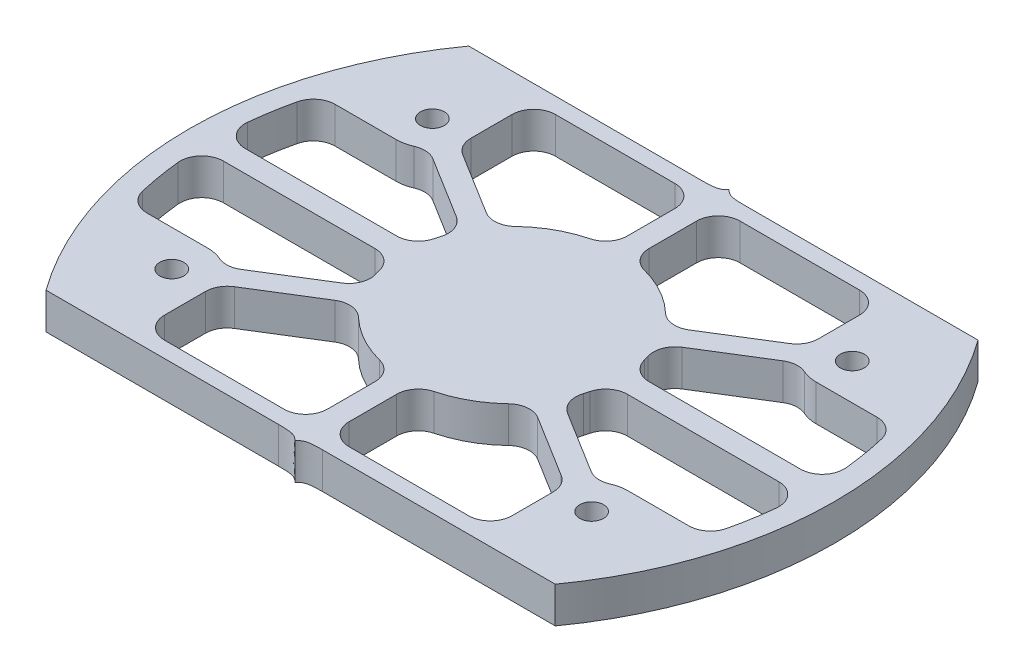
SolidWorks part; units mm, degrees
material "3.1355 (EN-AW 2024)"
ref_plane "Front" through (0, 0, 0) normal (0, 0, 1) x (1, 0, 0)
ref_plane "Top" through (0, 0, 0) normal (0, 1, 0) x (1, 0, 0)
ref_plane "Right" through (0, 0, 0) normal (1, 0, 0) x (0, 0, -1)
sketch "Эскиз1" plane through (0, 0, 0) normal (0, 1, 0) x (1, 0, 0)
  line L0 (0, 0) -> (0, 60) construction
  line L1 (0, 60) -> (10, 60) construction
  line L3 (79.1655, 0) -> (10, 0)
  line L4 (0, 30) -> (63.0426, 30) construction
  line L5 (10, 60) -> (79.1655, 60)
  line L6 (10, 0) -> (0, 0) construction
  line L7 (15.5828, 48) -> (73.5828, 48) construction
  line L8 (15.5828, 12) -> (73.5828, 12) construction
  line L9 (44.5828, 60) -> (44.5828, 0) construction
  arc A0 (10, 0) -> (10, 60) centre (50, 30) cw
  arc A1 (79.1655, 0) -> (79.1655, 60) centre (39.1655, 30) ccw
  point P5 (15.5828, 48)
  dimension "D3" = 50
  dimension "D1" = 60
  dimension "D2" = 12
  dimension "D4" = 38.84
  dimension "D5" = 58
extrude "Бобышка-Вытянуть1" add sketch "Эскиз1" along normal blind 5
sketch "Эскиз2" plane through (0, 5, 0) normal (0, 1, 0) x (1, 0, 0)
  line L4 (11.5292, 3) -> (77.6363, 3)
  line L5 (77.6363, 57) -> (11.5292, 57)
  line L6 (11.5292, 3) -> (77.6363, 3)
  line L7 (77.6363, 57) -> (11.5292, 57)
  arc A4 (11.5292, 57) -> (11.5292, 3) centre (50, 30) ccw
  arc A5 (77.6363, 3) -> (77.6363, 57) centre (39.1655, 30) ccw
  arc A6 (11.5292, 57) -> (11.5292, 3) centre (50, 30) ccw
  arc A7 (77.6363, 3) -> (77.6363, 57) centre (39.1655, 30) ccw
  dimension "D1" = 3
extrude "Вырез-Вытянуть1" cut sketch "Эскиз2" against normal through all
sketch "Эскиз3" plane through (0, 5, 0) normal (0, 1, 0) x (1, 0, 0)
  line L1 (89.1655, 30) -> (0, 30) construction
  circle A0 centre (15.5828, 48) radius 5
  circle A1 centre (73.5828, 48) radius 5
  arc A2 (79.1655, 0) -> (79.1655, 60) centre (39.1655, 30) ccw construction
  circle A3 centre (73.5828, 12) radius 5
  circle A4 centre (15.5828, 12) radius 5
  circle A5 centre (44.5828, 30) radius 15
  dimension "D1" = 10
  dimension "D2" = 10
  dimension "D3" = 30
extrude "Бобышка-Вытянуть2" add sketch "Эскиз3" against normal through all separate body
sketch "Эскиз4" plane through (0, 5, 0) normal (0, 1, 0) x (1, 0, 0)
  line L0 (77.6363, 57) -> (11.5292, 57) construction
  line L1 (11.5292, 3) -> (77.6363, 3) construction
  line L2 (77.6363, 57) -> (11.5292, 57) construction
  line L3 (11.5292, 3) -> (77.6363, 3) construction
  line L4 (44.5828, 45) -> (44.5828, 57) construction
  line L5 (31.8382, 37.9104) -> (19.831, 45.3632) construction
  line L6 (57.3274, 37.9104) -> (69.3346, 45.3632) construction
  line L7 (3, 30) -> (29.5828, 30) construction
  line L8 (86.1655, 30) -> (59.5828, 30) construction
  line L9 (57.3274, 22.0896) -> (69.3346, 14.6368) construction
  line L10 (31.8382, 22.0896) -> (19.831, 14.6368) construction
  line L11 (44.5828, 15) -> (44.5828, 3) construction
  line L12 (46.0828, 44.9248) -> (46.0828, 57)
  line L13 (32.6931, 39.1453) -> (20.4263, 46.7591)
  line L14 (58.0545, 36.5963) -> (70.3213, 44.2102)
  line L15 (56.4724, 20.8547) -> (68.7392, 13.2409)
  line L16 (43.0828, 15.0752) -> (43.0828, 3)
  line L17 (31.111, 23.4037) -> (18.8443, 15.7898)
  line L18 (43.0828, 44.9248) -> (43.0828, 57)
  line L19 (31.111, 36.5963) -> (18.8443, 44.2102)
  line L20 (56.4724, 39.1453) -> (68.7392, 46.7591)
  line L21 (58.0545, 23.4037) -> (70.3213, 15.7898)
  line L22 (46.0828, 15.0752) -> (46.0828, 3)
  line L23 (32.6931, 20.8547) -> (20.4263, 13.2409)
  line L24 (32.6292, 39.1849) -> (20.622, 46.6376) construction
  line L25 (31.0471, 36.636) -> (19.0399, 44.0887) construction
  line L26 (43.0828, 45) -> (43.0828, 57) construction
  line L27 (46.0828, 45) -> (46.0828, 57) construction
  line L28 (56.5363, 39.1849) -> (68.5435, 46.6376) construction
  line L29 (58.1184, 36.636) -> (70.1256, 44.0887) construction
  line L30 (58.1184, 23.364) -> (70.1256, 15.9113) construction
  line L31 (56.5363, 20.8151) -> (68.5435, 13.3624) construction
  line L32 (46.0828, 15) -> (46.0828, 3) construction
  line L33 (43.0828, 15) -> (43.0828, 3) construction
  line L34 (32.6292, 20.8151) -> (20.622, 13.3624) construction
  line L35 (31.0471, 23.364) -> (19.0399, 15.9113) construction
  line L36 (3.0239, 28.5) -> (29.658, 28.5)
  line L37 (86.1416, 31.5) -> (59.5076, 31.5)
  line L38 (3.0239, 31.5) -> (29.658, 31.5)
  line L39 (86.1416, 28.5) -> (59.5076, 28.5)
  line L40 (3, 31.5) -> (29.5828, 31.5) construction
  line L41 (3, 28.5) -> (29.5828, 28.5) construction
  line L42 (86.1655, 31.5) -> (59.5828, 31.5) construction
  line L43 (86.1655, 28.5) -> (59.5828, 28.5) construction
  line L44 (43.0828, 57) -> (46.0828, 57)
  line L45 (3.0239, 31.5) -> (2.4021, 31.5)
  line L46 (2.4021, 31.5) -> (2.4021, 28.5)
  line L47 (2.4021, 28.5) -> (3.0239, 28.5)
  line L48 (3.0239, 28.5) -> (2.938, 28.4918)
  line L49 (86.1416, 31.5) -> (86.6727, 31.5)
  line L50 (86.6727, 31.5) -> (86.6727, 28.5)
  line L51 (86.6727, 28.5) -> (86.1416, 28.5)
  line L52 (43.0828, 3) -> (46.0828, 3)
  arc A0 (11.5292, 57) -> (11.5292, 3) centre (50, 30) ccw construction
  circle A1 centre (44.5828, 30) radius 15
  arc A2 (43.0828, 15.0752) -> (46.0828, 15.0752) centre (44.5828, 30) ccw
  arc A3 (77.6363, 3) -> (77.6363, 57) centre (39.1655, 30) ccw construction
  arc A4 (11.5292, 57) -> (11.5292, 3) centre (50, 30) ccw construction
  arc A5 (77.6363, 3) -> (77.6363, 57) centre (39.1655, 30) ccw construction
  circle A6 centre (73.5828, 48) radius 5 construction
  circle A7 centre (73.5828, 12) radius 5 construction
  circle A8 centre (15.5828, 12) radius 5 construction
  circle A9 centre (15.5828, 48) radius 5 construction
  arc A10 (68.7392, 46.7591) -> (70.3213, 44.2102) centre (73.5828, 48) ccw
  arc A11 (70.3213, 15.7898) -> (68.7392, 13.2409) centre (73.5828, 12) ccw
  arc A12 (20.4263, 13.2409) -> (18.8443, 15.7898) centre (15.5828, 12) ccw
  arc A13 (18.8443, 44.2102) -> (20.4263, 46.7591) centre (15.5828, 48) ccw
  arc A14 (56.4724, 20.8547) -> (58.0545, 23.4037) centre (44.5828, 30) ccw
  arc A15 (31.111, 23.4037) -> (32.6931, 20.8547) centre (44.5828, 30) ccw
  arc A16 (59.5076, 28.5) -> (59.5076, 31.5) centre (44.5828, 30) ccw
  arc A17 (58.0545, 36.5963) -> (56.4724, 39.1453) centre (44.5828, 30) ccw
  arc A18 (29.658, 31.5) -> (29.658, 28.5) centre (44.5828, 30) ccw
  arc A19 (32.6931, 39.1453) -> (31.111, 36.5963) centre (44.5828, 30) ccw
  arc A20 (46.0828, 44.9248) -> (43.0828, 44.9248) centre (44.5828, 30) ccw
  circle M2 centre (44.5828, 30) radius 15
  dimension "D1" = 0
  dimension "D2" = 1.5
  dimension "D3" = 1.5
  dimension "D4" = 1.5
  dimension "D5" = 1.5
extrude "Бобышка-Вытянуть3" add sketch "Эскиз4" against normal through all contours A13 L19 L13 M2 | L44 L18 L12 M2 | A10 L20 L14 M2 | L51 L50 L49 L37 L39 M2 | A11 L21 L15 M2 | L16 L52 L22 M2 | A12 L23 L17 M2 | L46 L47 L36 L38 L45 M2
sketch "Эскиз5" plane through (0, 0, 0) normal (0, -1, 0) x (1, 0, 0)
  line L0 (20.5828, -3) -> (20.5828, -12)
  line L1 (11.5292, -3) -> (43.0828, -3) construction
  line L2 (44.5828, 0) -> (44.5828, -60) construction
  line L3 (0, -30) -> (89.1655, -30) construction
  line L4 (4.8336, -17) -> (15.5828, -17)
  line L5 (11.5292, -3) -> (20.5828, -3)
  line L6 (84.3319, -17) -> (73.5828, -17)
  line L7 (68.5828, -3) -> (68.5828, -12)
  line L8 (77.6363, -3) -> (68.5828, -3)
  line L9 (77.6363, -57) -> (68.5828, -57)
  line L10 (68.5828, -57) -> (68.5828, -48)
  line L11 (84.3319, -43) -> (73.5828, -43)
  line L12 (11.5292, -57) -> (20.5828, -57)
  line L13 (4.8336, -43) -> (15.5828, -43)
  line L14 (20.5828, -57) -> (20.5828, -48)
  arc A0 (79.1655, -60) -> (79.1655, 0) centre (39.1655, -30) ccw construction
  arc A1 (11.5292, -3) -> (3.0239, -28.5) centre (50, -30) ccw construction
  arc A3 (20.4263, -13.2409) -> (18.8443, -15.7898) centre (15.5828, -12) ccw construction
  arc A4 (11.5292, -3) -> (4.8336, -17) centre (50, -30) ccw
  arc A5 (20.5828, -12) -> (15.5828, -17) centre (15.5828, -12) ccw
  arc A6 (68.5828, -12) -> (73.5828, -17) centre (73.5828, -12) cw
  arc A7 (77.6363, -3) -> (84.3319, -17) centre (39.1655, -30) cw
  arc A8 (77.6363, -57) -> (84.3319, -43) centre (39.1655, -30) ccw
  arc A9 (68.5828, -48) -> (73.5828, -43) centre (73.5828, -48) ccw
  arc A10 (20.5828, -48) -> (15.5828, -43) centre (15.5828, -48) cw
  arc A11 (11.5292, -57) -> (4.8336, -43) centre (50, -30) cw
extrude "Бобышка-Вытянуть4" add sketch "Эскиз5" against normal through all
fillet "Скругление1" radius 3 40 edges at (70.3213, 2.5, -44.2102) (58.0545, 2.5, -36.5963) (59.5076, 2.5, -31.5) (59.5076, 2.5, -28.5) (58.0545, 2.5, -23.4037) (70.3213, 2.5, -15.7898) (84.3319, 2.5, -17) (86.1416, 2.5, -28.5) (86.1416, 2.5, -31.5) (84.3319, 2.5, -43) (56.4724, 2.5, -39.1453) (46.0828, 2.5, -44.9248) (46.0828, 2.5, -57) (68.5828, 2.5, -57) (68.7392, 2.5, -46.7591) (43.0828, 2.5, -44.9248) (43.0828, 2.5, -57) (20.5828, 2.5, -57) (32.6931, 2.5, -39.1453) (20.4263, 2.5, -46.7591) (31.111, 2.5, -36.5963) (18.8443, 2.5, -44.2102) (4.8336, 2.5, -43) (3.0239, 2.5, -31.5) (29.658, 2.5, -31.5) (29.658, 2.5, -28.5) (3.0239, 2.5, -28.5) (4.8336, 2.5, -17) (18.8443, 2.5, -15.7898) (31.111, 2.5, -23.4037) (43.0828, 2.5, -3) (20.5828, 2.5, -3) (20.4263, 2.5, -13.2409) (32.6931, 2.5, -20.8547) (43.0828, 2.5, -15.0752) (56.4724, 2.5, -20.8547) (46.0828, 2.5, -15.0752) (46.0828, 2.5, -3) (68.5828, 2.5, -3) (68.7392, 2.5, -13.2409)
hole_wizard "Отверстие обработанное метчиком M4x0.71" positions "Эскиз7" profile "Эскиз6" tap size "M4x0.7" standard "Ansi Metric" end condition through all
sketch "Эскиз7" plane through (0, 0, 0) normal (0, -1, 0) x (-1, 0, 0)
  point P0 (-15.5828, 12)
  point P3 (-73.5828, 12)
  point P6 (-73.5828, 48)
  point P9 (-15.5828, 48)
sketch "Эскиз6" plane through (15.5828, 0, -12) normal (1, 0, 0) x (0, 0, -1)
  line L0 (0, 0) -> (0, 5)
  line L1 (0, 5) -> (1.65, 5)
  line L2 (1.65, 5) -> (1.65, 0)
  line L5 (1.65, 0) -> (0, 0)
  line L11 (0, -6.35) -> (0, 107.95) construction
  dimension "Диаметр проходного сверла" = 3.3
  dimension "Глубина проходного сверла" = 5
cosmetic thread "Отверстие резьбы1" parameters "D2"=4
cosmetic thread "Отверстие резьбы2" parameters "D2"=4
cosmetic thread "Отверстие резьбы3" parameters "D2"=4
cosmetic thread "Отверстие резьбы4" parameters "D2"=4
sketch "Эскиз8" plane through (0, 0, 0) normal (0, -1, 0) x (1, 0, 0)
  line L0 (44.5828, 0) -> (44.5828, -60) construction
  line L1 (0, -30) -> (89.1655, -30) construction
  line L2 (9.4123, -0.8) -> (41.5278, -0.8)
  line L3 (79.1655, 0) -> (10, 0) construction
  line L4 (40.1307, -0.8) -> (42.9249, -0.8) construction
  line L5 (79.7532, -0.8) -> (47.6378, -0.8)
  line L6 (79.1655, 0) -> (10, 0)
  line L7 (79.1655, -60) -> (10, -60)
  line L8 (79.7532, -59.2) -> (47.6378, -59.2)
  line L9 (9.4123, -59.2) -> (41.5278, -59.2)
  arc A0 (79.1655, -60) -> (79.1655, 0) centre (39.1655, -30) ccw construction
  arc A1 (10, 0) -> (10, -60) centre (50, -30) ccw construction
  arc A2 (10, 0) -> (9.4123, -0.8) centre (50, -30) ccw
  arc A3 (79.7532, -0.8) -> (79.1655, 0) centre (39.1655, -30) ccw
  arc A4 (79.7532, -59.2) -> (79.1655, -60) centre (39.1655, -30) cw
  arc A5 (10, -60) -> (9.4123, -59.2) centre (50, -30) cw
  spline S0 degree 3 poles (44.5828, 0) (43.9591, -0.7036) (43.2742, -0.8) (41.5278, -0.8) knots 0 0 0 0 1 1 1 1
  spline S1 degree 3 poles (44.5828, 0) (45.2064, -0.7036) (45.8914, -0.8) (47.6378, -0.8) knots 0 0 0 0 1 1 1 1
  spline S2 degree 3 poles (44.5828, -60) (45.2064, -59.2964) (45.8914, -59.2) (47.6378, -59.2) knots 0 0 0 0 1 1 1 1
  spline S3 degree 3 poles (44.5828, -60) (43.9591, -59.2964) (43.2742, -59.2) (41.5278, -59.2) knots 0 0 0 0 1 1 1 1
  dimension "D1" = 0.8
extrude "Вырез-Вытянуть2" cut sketch "Эскиз8" against normal through all contours S0 L6 A2 L2 | L6 S1 L5 A3 | L7 S3 L9 A5 | S2 L7 A4 L8
equation "\"D2@Эскиз3\"=\"D1@Эскиз3\""
